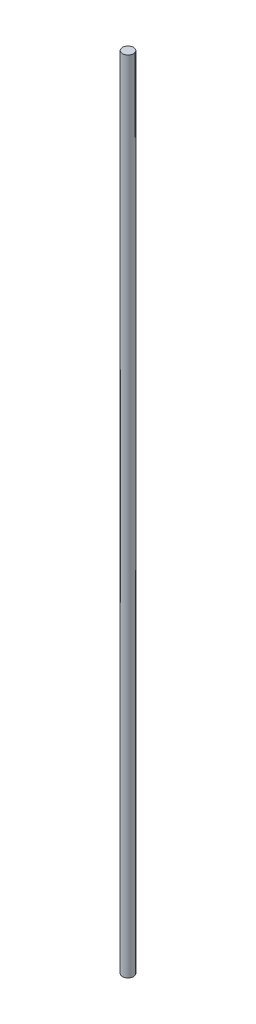
SolidWorks part; units mm, degrees
ref_plane "Front Plane" through (0, 0, 0) normal (0, 0, 1) x (1, 0, 0)
ref_plane "Top Plane" through (0, 0, 0) normal (0, 1, 0) x (1, 0, 0)
ref_plane "Right Plane" through (0, 0, 0) normal (1, 0, 0) x (0, 0, -1)
sketch "Sketch1" plane through (0, 0, 0) normal (0, 1, 0) x (1, 0, 0)
  circle A0 centre (0, 0) radius 4
  dimension "D1" = 8
extrude "Boss-Extrude1" add sketch "Sketch1" along normal blind 580
